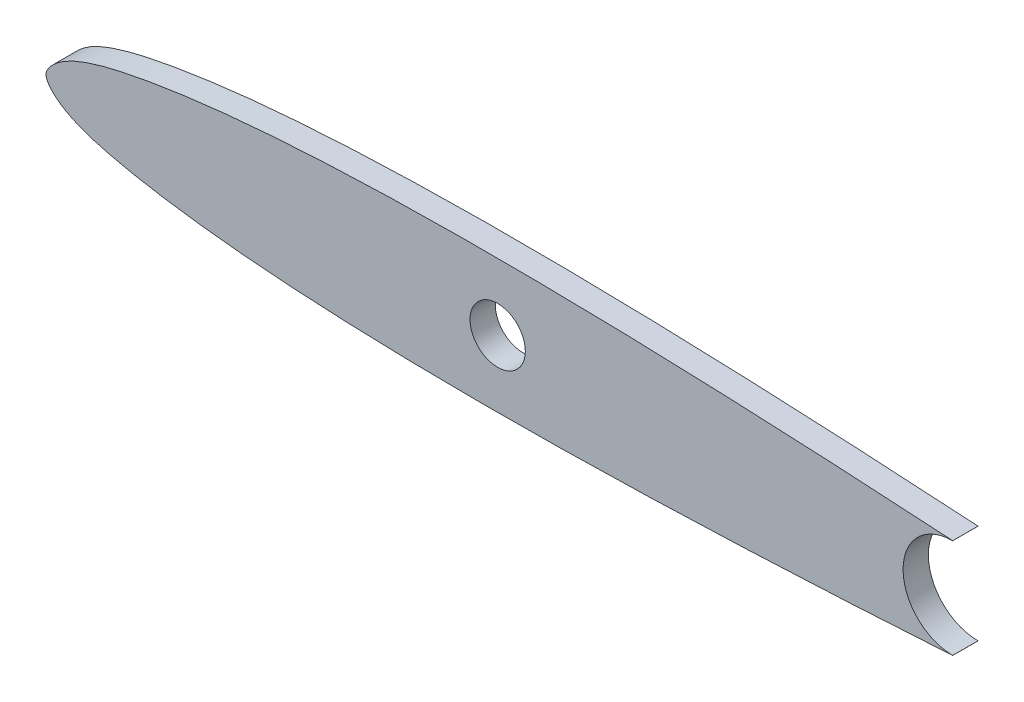
SolidWorks part; units mm, degrees
material "Balsa"
ref_plane "Front Plane" through (0, 0, 0) normal (0, 0, 1) x (1, 0, 0)
ref_plane "Top Plane" through (0, 0, 0) normal (0, 1, 0) x (1, 0, 0)
ref_plane "Right Plane" through (0, 0, 0) normal (1, 0, 0) x (0, 0, -1)
sketch "Sketch5" plane through (0, 0, 0) normal (0, 0, 1) x (1, 0, 0)
  spline S1 degree 3 poles (132.6352, -0.1273) (134.1653, 0) (132.6352, 0.1273) (131.3812, 0.3396) (128.335, 0.6651) (124.5922, 1.0691) (119.7155, 1.5433) (113.99, 2.0665) (107.4406, 2.6287) (100.2046, 3.2135) (92.3972, 3.7974) (84.1546, 4.3633) (75.6172, 4.885) (66.9312, 5.3404) (58.2449, 5.7025) (51.0726, 5.9117) (45.4464, 6.0078) (41.3533, 6.0419) (37.3694, 6.0372) (33.5118, 5.9859) (29.7974, 5.8959) (26.2422, 5.7599) (22.8612, 5.583) (19.6686, 5.361) (16.6778, 5.0976) (13.9025, 4.7906) (11.3544, 4.4458) (9.0435, 4.072) (6.9793, 3.671) (5.1685, 3.2442) (3.6198, 2.7772) (2.3364, 2.2613) (1.3302, 1.692) (0.6066, 1.0976) (0.1547, 0.5528) (-0.0633, 0) (0.1547, -0.5528) (0.6066, -1.0976) (1.3302, -1.692) (2.3364, -2.2613) (3.6198, -2.7772) (5.1685, -3.2442) (6.9793, -3.671) (9.0435, -4.072) (11.3544, -4.4458) (13.9025, -4.7906) (16.6778, -5.0976) (19.6686, -5.361) (22.8612, -5.583) (26.2422, -5.7599) (29.7974, -5.8959) (33.5118, -5.9859) (37.3694, -6.0372) (41.3533, -6.0419) (45.4464, -6.0078) (51.0726, -5.9117) (58.2449, -5.7025) (66.9312, -5.3404) (75.6172, -4.885) (84.1546, -4.3633) (92.3972, -3.7974) (100.2046, -3.2135) (107.4406, -2.6287) (113.99, -2.0665) (119.7155, -1.5433) (124.5922, -1.0691) (128.335, -0.6651) (131.3812, -0.3396) (132.6352, -0.1273) (134.1653, 0) (132.6352, 0.1273) knots -0.018944 -0.008488 -0.002133 0 0.002133 0.008488 0.018944 0.033319 0.051356 0.072756 0.097141 0.124097 0.153163 0.183834 0.215589 0.247878 0.280151 0.31186 0.327333 0.342463 0.357187 0.371448 0.385183 0.398331 0.410845 0.422673 0.433769 0.44409 0.453589 0.46224 0.47001 0.476871 0.482833 0.487909 0.492155 0.495592 0.498196 0.5 0.501804 0.504408 0.507845 0.512091 0.517167 0.523129 0.52999 0.53776 0.546411 0.55591 0.566231 0.577327 0.589155 0.601669 0.614817 0.628552 0.642813 0.657537 0.672667 0.68814 0.719849 0.752122 0.784411 0.816166 0.846837 0.875903 0.902859 0.927244 0.948644 0.966681 0.981056 0.991512 0.997867 1 1.002133 1.008488 1.018944 only from (133.858, 0) to (133.858, 0)
  dimension "D1" = 133.858
extrude "Boss-Extrude1" add sketch "Sketch5" along normal blind 2.286
sketch "Sketch6" plane through (0, 0, 2.286) normal (0, 0, 1) x (1, 0, 0)
  line L0 (0, 0) -> (40.8267, 0)
  line L1 (133.858, 0) -> (77.978, 0)
  line L2 (81.9608, -5.493) -> (81.9608, -4.4876)
  line L3 (81.9608, 6.5472) -> (133.858, 6.5472)
  line L4 (133.858, 6.5472) -> (133.858, -10.9089)
  line L5 (133.858, -10.9089) -> (81.9608, -5.493)
  line L6 (81.9608, 4.4876) -> (81.9608, 6.5472)
  circle A0 centre (40.8267, 0) radius 2.5
  arc A1 (81.9608, 4.4876) -> (81.9608, -4.4876) centre (81.9608, 0) ccw
  spline S0 degree 3 poles (132.6352, -0.1273) (134.1653, 0) (132.6352, 0.1273) (131.3812, 0.3396) (128.335, 0.6651) (124.5922, 1.0691) (119.7155, 1.5433) (113.99, 2.0665) (107.4406, 2.6287) (100.2046, 3.2135) (92.3972, 3.7974) (84.1546, 4.3633) (75.6172, 4.885) (66.9312, 5.3404) (58.2449, 5.7025) (51.0726, 5.9117) (45.4464, 6.0078) (41.3533, 6.0419) (37.3694, 6.0372) (33.5118, 5.9859) (29.7974, 5.8959) (26.2422, 5.7599) (22.8612, 5.583) (19.6686, 5.361) (16.6778, 5.0976) (13.9025, 4.7906) (11.3544, 4.4458) (9.0435, 4.072) (6.9793, 3.671) (5.1685, 3.2442) (3.6198, 2.7772) (2.3364, 2.2613) (1.3302, 1.692) (0.6066, 1.0976) (0.1547, 0.5528) (-0.0633, 0) (0.1547, -0.5528) (0.6066, -1.0976) (1.3302, -1.692) (2.3364, -2.2613) (3.6198, -2.7772) (5.1685, -3.2442) (6.9793, -3.671) (9.0435, -4.072) (11.3544, -4.4458) (13.9025, -4.7906) (16.6778, -5.0976) (19.6686, -5.361) (22.8612, -5.583) (26.2422, -5.7599) (29.7974, -5.8959) (33.5118, -5.9859) (37.3694, -6.0372) (41.3533, -6.0419) (45.4464, -6.0078) (51.0726, -5.9117) (58.2449, -5.7025) (66.9312, -5.3404) (75.6172, -4.885) (84.1546, -4.3633) (92.3972, -3.7974) (100.2046, -3.2135) (107.4406, -2.6287) (113.99, -2.0665) (119.7155, -1.5433) (124.5922, -1.0691) (128.335, -0.6651) (131.3812, -0.3396) (132.6352, -0.1273) (134.1653, 0) (132.6352, 0.1273) knots -0.018944 -0.008488 -0.002133 0 0.002133 0.008488 0.018944 0.033319 0.051356 0.072756 0.097141 0.124097 0.153163 0.183834 0.215589 0.247878 0.280151 0.31186 0.327333 0.342463 0.357187 0.371448 0.385183 0.398331 0.410845 0.422673 0.433769 0.44409 0.453589 0.46224 0.47001 0.476871 0.482833 0.487909 0.492155 0.495592 0.498196 0.5 0.501804 0.504408 0.507845 0.512091 0.517167 0.523129 0.52999 0.53776 0.546411 0.55591 0.566231 0.577327 0.589155 0.601669 0.614817 0.628552 0.642813 0.657537 0.672667 0.68814 0.719849 0.752122 0.784411 0.816166 0.846837 0.875903 0.902859 0.927244 0.948644 0.966681 0.981056 0.991512 0.997867 1 1.002133 1.008488 1.018944 only from (133.858, 0) to (133.858, 0) construction
  dimension "D2" = 5
  dimension "D1" = 40.8267
  dimension "D3" = 55.88
extrude "Cut-Extrude1" cut sketch "Sketch6" against normal through all
